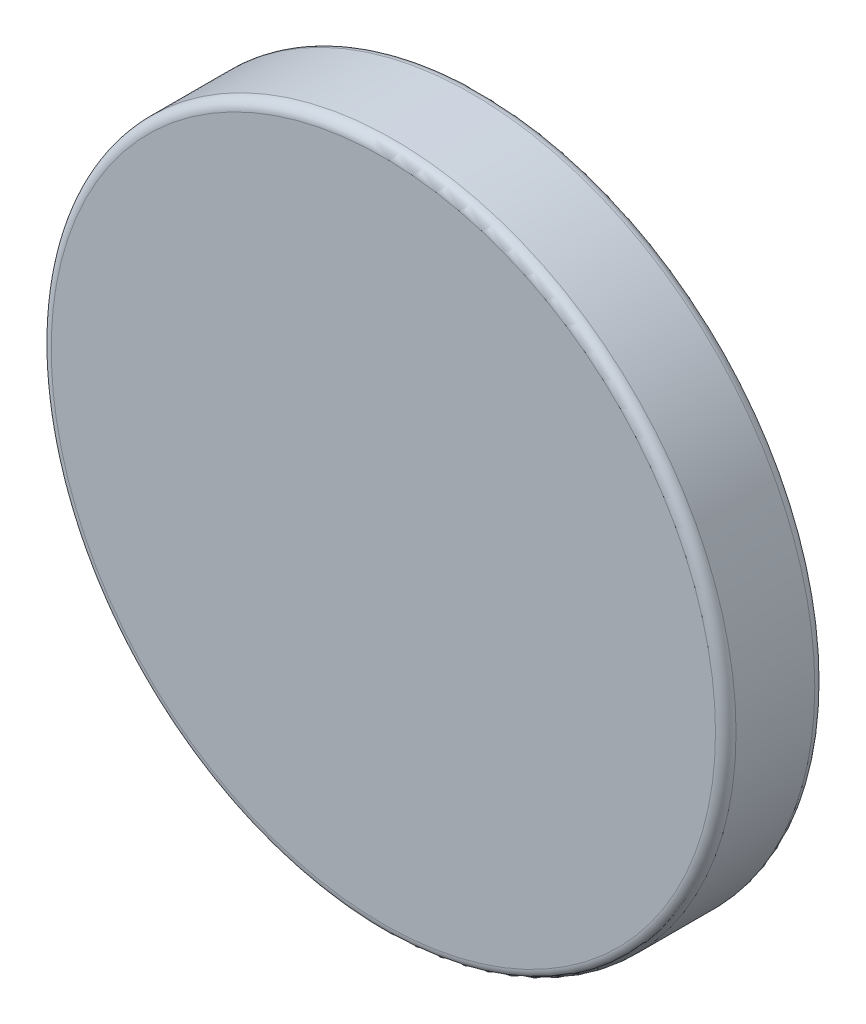
SolidWorks part; units mm, degrees
material "Nikl"
ref_plane "Přední rovina" through (0, 0, 0) normal (0, 0, 1) x (1, 0, 0)
ref_plane "Horní rovina" through (0, 0, 0) normal (0, 1, 0) x (1, 0, 0)
ref_plane "Pravá rovina" through (0, 0, 0) normal (1, 0, 0) x (0, 0, -1)
sketch "Skica1" plane through (0, 0, 0) normal (0, 0, 1) x (1, 0, 0)
  circle A0 centre (0, 0) radius 5
  dimension "D1" = 10
extrude "Přidat vysunutím1" add sketch "Skica1" along normal blind 1.45
fillet "Zaoblit1" radius 0.15 2 edges at (5, 0, 0) (5, 0, 1.45)
